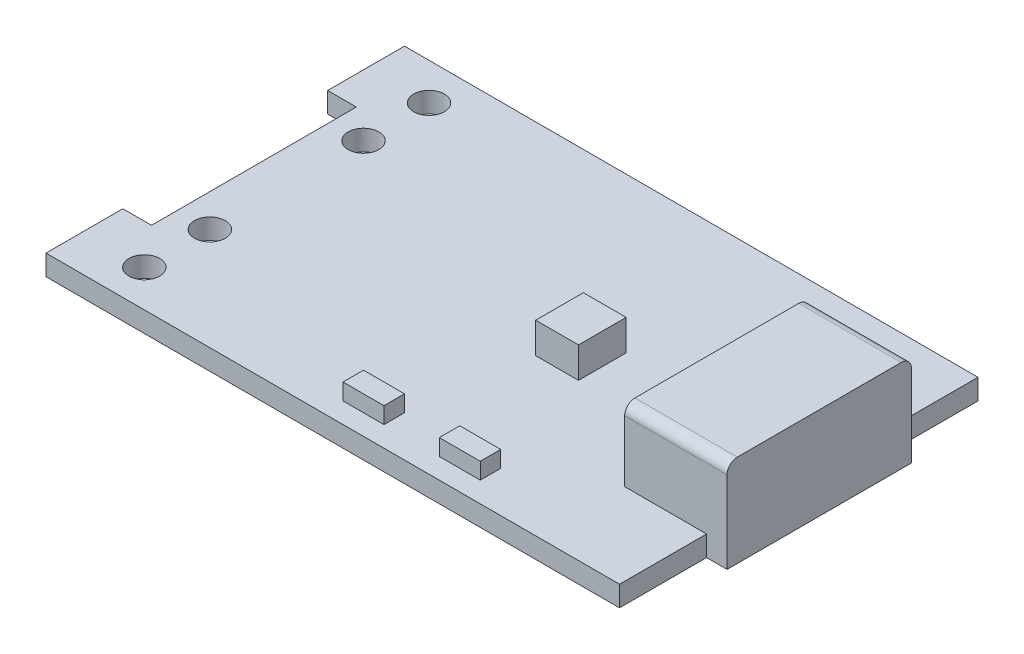
SolidWorks part; units mm, degrees
ref_plane "前视基准面" through (0, 0, 0) normal (0, 0, 1) x (1, 0, 0)
ref_plane "上视基准面" through (0, 0, 0) normal (0, 1, 0) x (1, 0, 0)
ref_plane "右视基准面" through (0, 0, 0) normal (1, 0, 0) x (0, 0, -1)
sketch "草图1" plane through (0, 0, 0) normal (0, 1, 0) x (1, 0, 0)
  line L1 (-14, 8.75) -> (14, 8.75)
  line L2 (-14, 8.75) -> (-14, -8.75)
  line L3 (-14, -8.75) -> (14, -8.75)
  line L4 (14, 8.75) -> (14, -8.75)
  line L5 (-14, 8.75) -> (14, -8.75) construction
  line L6 (-14, -8.75) -> (14, 8.75) construction
  point P0 (0, 0)
  dimension "D1" = 28
  dimension "D2" = 17.5
extrude "凸台-拉伸1" add sketch "草图1" along normal blind 1
sketch "草图2" plane through (0, 1, 0) normal (0, 1, 0) x (1, 0, 0)
  line L0 (14, 0) -> (0, 0) construction
  line L1 (10, 4.5) -> (15, 4.5)
  line L2 (10, 4.5) -> (10, -4.5)
  line L3 (10, -4.5) -> (15, -4.5)
  line L4 (15, 4.5) -> (15, -4.5)
  line L5 (14, -8.75) -> (14, 8.75) construction
  dimension "D1" = 5
  dimension "D2" = 9
  dimension "D3" = 1
extrude "凸台-拉伸2" add sketch "草图2" along normal blind 4.5 from surface at -1 starting at face at (0, 0, 0)
fillet "圆角1" radius 0.5 2 edges at (12.5, 4.5, -4.5) (12.5, 4.5, 4.5)
sketch "草图3" plane through (0, 1, 0) normal (0, 1, 0) x (1, 0, 0)
  line L1 (2.2905, 1.1937) -> (4.3794, 1.1937)
  line L2 (2.2905, 1.1937) -> (2.2905, -1.134)
  line L3 (2.2905, -1.134) -> (4.3794, -1.134)
  line L4 (4.3794, 1.1937) -> (4.3794, -1.134)
extrude "凸台-拉伸3" add sketch "草图3" along normal blind 1.5
sketch "草图6" plane through (0, 1, 0) normal (0, 1, 0) x (1, 0, 0)
  line L0 (-14, 8.75) -> (-14, -8.75) construction
  line L1 (-14, 5) -> (-12.6, 5)
  line L2 (-14, 5) -> (-14, -5)
  line L3 (-14, -5) -> (-12.6, -5)
  line L4 (-12.6, 5) -> (-12.6, -5)
  line L5 (0, 0) -> (-14, 0) construction
  line L6 (15, -4) -> (15, 4) construction
  dimension "D1" = 10
  dimension "D2" = 27.6
extrude "切除-拉伸2" cut sketch "草图6" against normal through all
sketch "草图4" plane through (0, 1, 0) normal (0, 1, 0) x (1, 0, 0)
  line L0 (0, 0) -> (-14, 0) construction
  line L3 (-14, 8.75) -> (-14, 5) construction
  line L4 (-11, 6.95) -> (-11, -6.95) construction
  line L5 (14, 8.75) -> (-14, 8.75) construction
  circle A0 centre (-11, 6.95) radius 0.75
  circle A1 centre (-11, 3.75) radius 0.75
  circle A2 centre (-11, -3.75) radius 0.75
  circle A3 centre (-11, -6.95) radius 0.75
  dimension "D1" = 1.5
  dimension "D2" = 3
  dimension "D3" = 3.2
  dimension "D4" = 5
extrude "切除-拉伸1" cut sketch "草图4" against normal through all
sketch "草图5" plane through (0, 1, 0) normal (0, 1, 0) x (1, 0, 0)
  line L0 (14, -8.75) -> (14, -4.5) construction
  line L1 (4.2, -6.75) -> (6.2, -6.75)
  line L2 (4.2, -6.75) -> (4.2, -7.75)
  line L3 (4.2, -7.75) -> (6.2, -7.75)
  line L4 (6.2, -6.75) -> (6.2, -7.75)
  line L5 (-14, -8.75) -> (14, -8.75) construction
  dimension "D1" = 2
  dimension "D2" = 1
  dimension "D3" = 9.8
  dimension "D4" = 2
extrude "凸台-拉伸4" add sketch "草图5" along normal blind 1.8 from surface at -1 starting at face at (-11, 0, -6.2)
pattern_linear "阵列(线性)1" count 2 spacing 4.7 along (-1, 0, 0) of "凸台-拉伸4"
